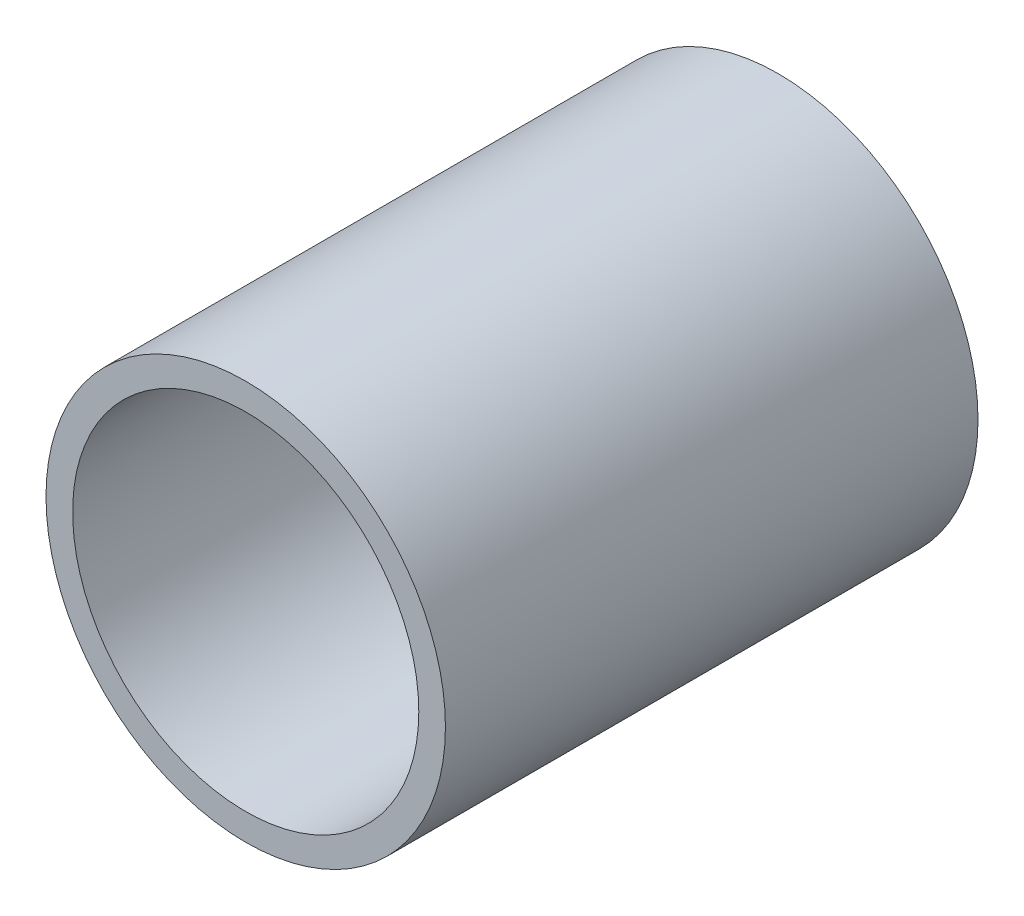
SolidWorks part; units mm, degrees
ref_plane "Front Plane" through (0, 0, 0) normal (0, 0, 1) x (1, 0, 0)
ref_plane "Top Plane" through (0, 0, 0) normal (0, 1, 0) x (1, 0, 0)
ref_plane "Right Plane" through (0, 0, 0) normal (1, 0, 0) x (0, 0, -1)
sketch "Sketch4" plane through (0, 0, 0) normal (0, 0, 1) x (1, 0, 0)
  circle A0 centre (0, 0) radius 15
  dimension "D1" = 30
extrude "Boss-Extrude3" add sketch "Sketch4" along normal blind 40 contours A0
shell "Shell1" thickness 2
